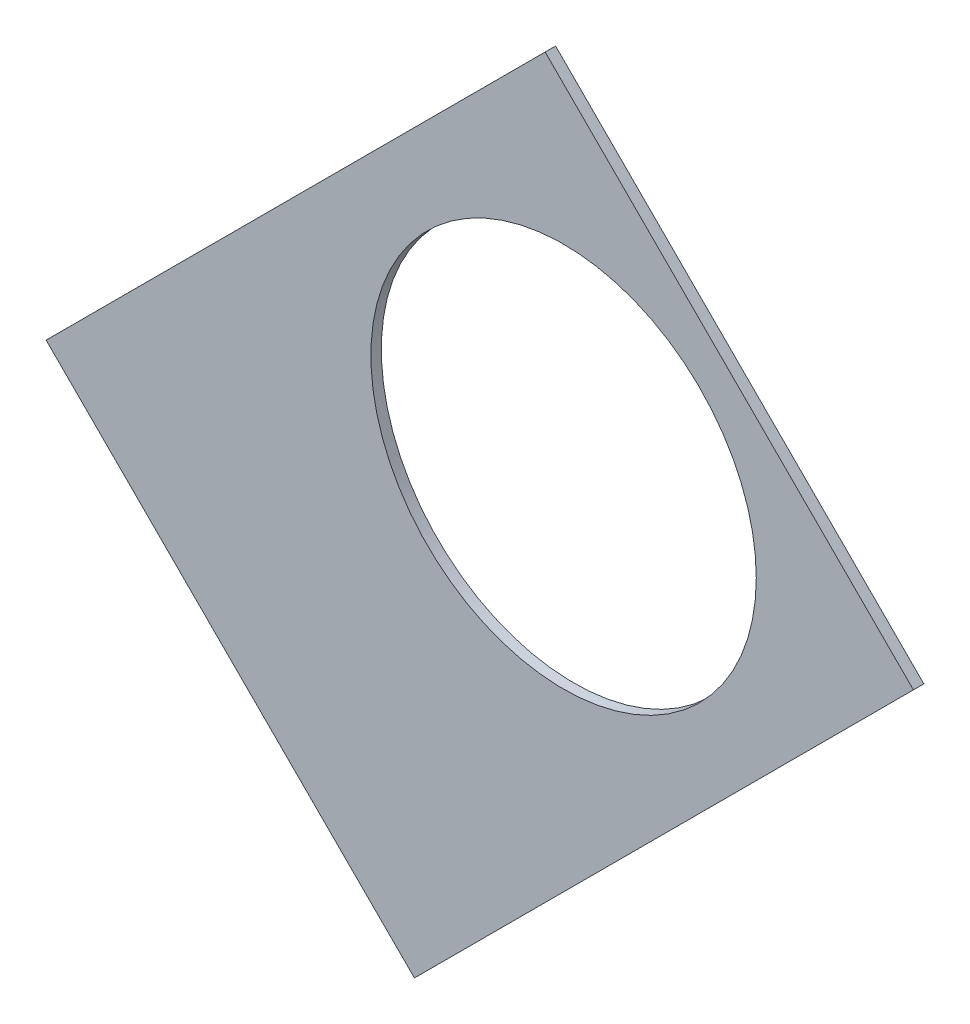
SolidWorks part; units mm, degrees
material "Copper"
ref_plane "Front Plane" through (0, 0, 0) normal (0, 0, 1) x (1, 0, 0)
ref_plane "Top Plane" through (0, 0, 0) normal (0, 1, 0) x (1, 0, 0)
ref_plane "Right Plane" through (0, 0, 0) normal (1, 0, 0) x (0, 0, -1)
sketch "Sketch1" plane through (0, 0, 0) normal (0, 0, 1) x (1, 0, 0)
  line L0 (0, 0) -> (320.3893, 0) construction
  line L1 (0, 0) -> (155.5285, 155.5285) construction
  line L2 (67.2115, 76.1917) -> (8.6967, 17.6769)
  line L3 (8.6967, 17.6769) -> (7.229, 14.1336)
  line L4 (101.4014, -6.35) -> (18.6489, -6.35)
  line L5 (15.1056, -4.8823) -> (18.6489, -6.35)
  line L6 (88.6729, 6.35) -> (27.8605, 6.35)
  line L9 (67.1914, 58.2111) -> (24.1905, 15.2102)
  line L10 (0, 0) -> (40.4486, 97.6516) construction
  line L11 (0, 0) -> (123.4567, -51.1374) construction
  line L18 (8.6967, 17.6769) -> (13.294, 8.6183) construction
  line L19 (18.6489, -6.35) -> (15.4943, 3.3063) construction
  line L20 (27.8605, 6.35) -> (27.7442, 6.7059) construction
  line L21 (24.1905, 15.2102) -> (24.3599, 14.8764) construction
  arc A0 (7.229, 14.1336) -> (15.1056, -4.8823) centre (0, 0) cw
  arc A1 (67.2115, 76.1917) -> (101.4014, -6.35) centre (0, 0) cw
  arc A2 (24.1905, 15.2102) -> (27.8605, 6.35) centre (0, 0) cw
  arc A3 (67.1914, 58.2111) -> (88.6729, 6.35) centre (0, 0) cw
  arc A8 (13.294, 8.6183) -> (15.4943, 3.3063) centre (0, 0) cw construction
  arc A9 (24.3599, 14.8764) -> (27.7442, 6.7059) centre (0, 0) cw construction
  dimension "D1" = 45
  dimension "D3" = 6.35
  dimension "D4" = 15.875
  dimension "D7" = 22.5
  dimension "D8" = 101.6
  dimension "D11" = 12.7
  dimension "D12" = 12.7
  dimension "D2" = 6.35
  dimension "D5" = 67.5
  dimension "D9" = 1.27
  dimension "D10" = 1.27
  dimension "D6" = 12.7
extrude "Boss-Extrude1" add sketch "Sketch1" along normal blind 0.254
sketch "Sketch2" plane through (0, 0, 0.254) normal (0, 0, 1) x (1, 0, 0)
  line L0 (0, 0) -> (101.6, 0) construction
  line L1 (0, 0) -> (71.842, 71.842) construction
  line L3 (0, 0) -> (22.225, 0) construction
  line L4 (0, 0) -> (15.7154, 15.7154) construction
  line L5 (0, 0) -> (95.25, 0) construction
  line L6 (0, 0) -> (92.0044, 24.6525) construction
  arc A0 (101.4014, -6.35) -> (67.2115, 76.1917) centre (0, 0) ccw construction
  circle A1 centre (22.225, 0) radius 4.699
  arc A2 (15.1056, -4.8823) -> (7.229, 14.1336) centre (0, 0) ccw construction
  circle A3 centre (36.195, 0) radius 4.699
  circle A4 centre (61.722, 0) radius 4.699
  circle A5 centre (75.692, 0) radius 4.699
  circle A6 centre (95.25, 0) radius 4.699
  circle A7 centre (15.7154, 15.7154) radius 4.699
  circle A8 centre (25.5937, 25.5937) radius 4.699
  circle A9 centre (43.644, 43.644) radius 4.699
  circle A10 centre (53.5223, 53.5223) radius 4.699
  circle A11 centre (92.0044, 24.6525) radius 4.699
  circle A12 centre (82.4889, 47.625) radius 4.699
  circle A13 centre (67.3519, 67.3519) radius 4.699
  dimension "D3" = 9.398
  dimension "D1" = 45
  dimension "D2" = 6.35
  dimension "D4" = 6.35
  dimension "D5" = 13.97
  dimension "D7" = 13.97
  dimension "D8" = 19.558
  dimension "D9" = 45
  dimension "D10" = 15
  dimension "D11" = 25.527
  dimension "D6" = 2
extrude "Cut-Extrude1" cut sketch "Sketch2" against normal through all
sketch "Sketch3" plane through (0, 0, 0.254) normal (0, 0, 1) x (1, 0, 0)
  line L0 (15.2664, 24.2467) -> (17.0625, 26.0427)
  line L1 (15.2664, 24.2467) -> (15.7154, 23.7977)
  line L2 (17.0625, 26.0427) -> (17.5115, 25.5937)
  line L3 (15.7154, 23.7977) -> (17.5115, 25.5937)
  line L4 (67.2115, 76.1917) -> (8.6967, 17.6769) construction
  line L5 (44.9911, 53.9713) -> (43.195, 52.1753)
  line L6 (44.9911, 53.9713) -> (45.4401, 53.5223)
  line L7 (43.195, 52.1753) -> (43.644, 51.7263)
  line L8 (45.4401, 53.5223) -> (43.644, 51.7263)
  line L9 (27.94, -6.35) -> (30.48, -6.35)
  line L10 (27.94, -6.35) -> (27.94, -5.715)
  line L11 (30.48, -6.35) -> (30.48, -5.715)
  line L12 (27.94, -5.715) -> (30.48, -5.715)
  line L13 (18.6489, -6.35) -> (101.4014, -6.35) construction
  line L14 (67.437, -6.35) -> (69.977, -6.35)
  line L15 (67.437, -6.35) -> (67.437, -5.715)
  line L16 (69.977, -6.35) -> (69.977, -5.715)
  line L17 (67.437, -5.715) -> (69.977, -5.715)
  line L18 (29.2307, 38.211) -> (31.0268, 40.007)
  line L19 (29.2307, 38.211) -> (29.6797, 37.762)
  line L20 (31.0268, 40.007) -> (31.4758, 39.558)
  line L21 (29.6797, 37.762) -> (31.4758, 39.558)
  line L22 (56.845, 65.8253) -> (55.049, 64.0292)
  line L23 (56.845, 65.8253) -> (57.294, 65.3763)
  line L24 (55.049, 64.0292) -> (55.498, 63.5802)
  line L25 (57.294, 65.3763) -> (55.498, 63.5802)
  line L26 (47.6885, -6.35) -> (50.2285, -6.35)
  line L27 (47.6885, -6.35) -> (47.6885, -5.715)
  line L28 (50.2285, -6.35) -> (50.2285, -5.715)
  line L29 (47.6885, -5.715) -> (50.2285, -5.715)
  line L30 (84.201, -6.35) -> (86.741, -6.35)
  line L31 (84.201, -6.35) -> (84.201, -5.715)
  line L32 (86.741, -6.35) -> (86.741, -5.715)
  line L33 (84.201, -5.715) -> (86.741, -5.715)
  line L34 (0, 0) -> (100.7308, 13.2615) construction
  line L35 (0, 0) -> (93.8662, 38.8806) construction
  line L36 (0, 0) -> (80.6047, 61.8502) construction
  line L37 (0, 0) -> (101.6, 0) construction
  line L38 (99.9355, 14.4377) -> (100.267, 11.9194)
  line L39 (99.9355, 14.4377) -> (101.1946, 14.6035)
  line L40 (100.267, 11.9194) -> (101.5261, 12.0852)
  line L41 (101.1946, 14.6035) -> (101.5261, 12.0852)
  line L42 (99.9355, 14.4377) -> (101.5261, 12.0852) construction
  line L43 (100.267, 11.9194) -> (101.1946, 14.6035) construction
  line L44 (93.7655, 37.4643) -> (94.9388, 37.9503)
  line L45 (93.7655, 37.4643) -> (92.7935, 39.811)
  line L46 (94.9388, 37.9503) -> (93.9668, 40.297)
  line L47 (92.7935, 39.811) -> (93.9668, 40.297)
  line L48 (93.7655, 37.4643) -> (93.9668, 40.297) construction
  line L49 (94.9388, 37.9503) -> (92.7935, 39.811) construction
  line L50 (79.3278, 62.4712) -> (80.874, 60.456)
  line L51 (79.3278, 62.4712) -> (80.3354, 63.2443)
  line L52 (80.874, 60.456) -> (81.8816, 61.2292)
  line L53 (80.3354, 63.2443) -> (81.8816, 61.2292)
  line L54 (79.3278, 62.4712) -> (81.8816, 61.2292) construction
  line L55 (80.874, 60.456) -> (80.3354, 63.2443) construction
  line L56 (13.5939, 7.0054) -> (14.5659, 4.6588)
  line L57 (13.5939, 7.0054) -> (14.7672, 7.4914)
  line L58 (14.5659, 4.6588) -> (15.7393, 5.1448)
  line L59 (14.7672, 7.4914) -> (15.7393, 5.1448)
  line L60 (13.5939, 7.0054) -> (15.7393, 5.1448) construction
  line L61 (14.5659, 4.6588) -> (14.7672, 7.4914) construction
  circle A0 centre (15.7154, 15.7154) radius 4.699 construction
  circle A1 centre (43.644, 43.644) radius 4.699 construction
  circle A2 centre (22.225, 0) radius 4.699 construction
  circle A3 centre (61.722, 0) radius 4.699 construction
  arc A4 (101.4014, -6.35) -> (67.2115, 76.1917) centre (0, 0) ccw construction
  arc A9 (15.1056, -4.8823) -> (7.229, 14.1336) centre (0, 0) ccw construction
  circle A10 centre (36.195, 0) radius 4.699 construction
  circle A11 centre (75.692, 0) radius 4.699 construction
  circle A12 centre (25.5937, 25.5937) radius 4.699 construction
  circle A13 centre (53.5223, 53.5223) radius 4.699 construction
  point P75 (14.6666, 6.0751)
  dimension "D2" = 5.715
  dimension "D3" = 2.54
  dimension "D6" = 5.715
  dimension "D8" = 0.635
  dimension "D9" = 5.715
  dimension "D12" = 5.715
  dimension "D4" = 7.5
  dimension "D5" = 22.5
  dimension "D7" = 37.5
  dimension "D10" = 90
  dimension "D11" = 1.27
  dimension "D14" = 0.635
  dimension "D15" = 90
  dimension "D18" = 0.635
  dimension "D19" = 90
  dimension "D22" = 0.635
  dimension "D20" = 1.27
  dimension "D17" = 0.635
  dimension "D13" = 11.4935
  dimension "D16" = 8.509
  dimension "D21" = 11.4935
  dimension "D23" = 8.509
extrude "Cut-Extrude2" cut sketch "Sketch3" against normal through all
sketch "Sketch5" plane through (0, 0, 0.254) normal (0, 0, 1) x (1, 0, 0)
  line L0 (30.1288, 40.9051) -> (42.297, 53.0733)
  line L1 (30.1288, 40.9051) -> (40.9051, 30.1288)
  line L2 (42.297, 53.0733) -> (53.0733, 42.297)
  line L3 (45.4401, 53.5223) -> (44.9911, 53.9713) construction
  line L4 (40.9051, 30.1288) -> (53.0733, 42.297)
  line L8 (43.195, 52.1753) -> (31.0268, 40.007) construction
  line L10 (29.2307, 38.211) -> (29.6797, 37.762) construction
  dimension "D1" = 15.24
  dimension "D2" = 1.27
  dimension "D3" = 2.54
  dimension "D4" = 2.54
extrude "Cut-Extrude5" cut sketch "Sketch5" against normal through all flip side to cut
equation "\"cSep\"= 1.005"
equation "\"D11@Sketch2\"=\"cSep\""
equation "\"cSep2\"= \"D8@Sketch2\""
equation "\"D13@Sketch3\"=\"cSep\"/2-.05"
equation "\"D16@Sketch3\"=\"cSep2\"/2-.05"
equation "\"D21@Sketch3\"=\"cSep\"/2-.05"
equation "\"D23@Sketch3\"=\"cSep2\"/2-.05"
